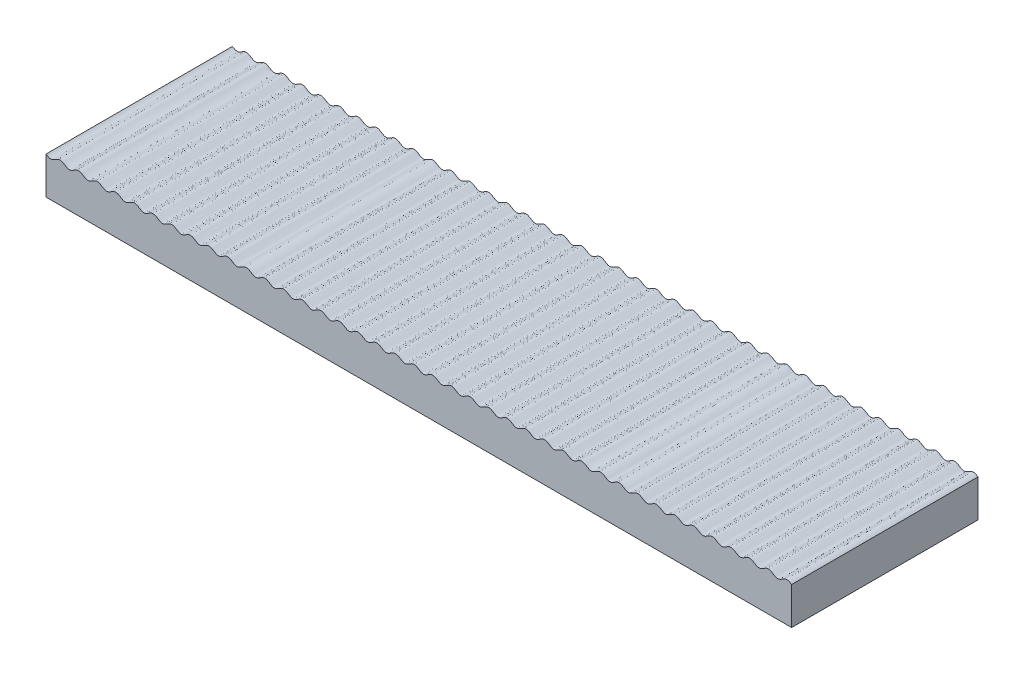
SolidWorks part; units mm, degrees
ref_plane "Ebene vorne" through (0, 0, 0) normal (0, 0, 1) x (1, 0, 0)
ref_plane "Ebene oben" through (0, 0, 0) normal (0, 1, 0) x (1, 0, 0)
ref_plane "Ebene rechts" through (0, 0, 0) normal (1, 0, 0) x (0, 0, -1)
sketch "Skizze1" plane through (0, 0, 0) normal (0, 0, 1) x (1, 0, 0)
  line L0 (0, 10) -> (0, 0)
  line L1 (0, 0) -> (200, 0)
  line L3 (0, 10) -> (200, 10) construction
  line L4 (200, 0) -> (200, 10)
  line L5 (0, 10) -> (0, 0) construction
  line L6 (5, 10) -> (5, 0) construction
  line L7 (0, 9.5001) -> (200, 9.5001) construction
  spline S0 degree 4 poles (-19.8, 9.8758) (-19.7067, 9.8176) (-19.5164, 9.7081) (-19.2314, 9.5662) (-18.8203, 9.473) (-18.326, 9.5323) (-17.8147, 9.7864) (-17.3529, 10.1027) (-16.8627, 10.3873) (-16.4131, 10.513) (-16.0482, 10.5034) (-15.6367, 10.3799) (-15.2035, 10.1377) (-14.7965, 9.8623) (-14.3634, 9.6201) (-13.955, 9.4976) (-13.5973, 9.4869) (-13.171, 9.601) (-12.7145, 9.855) (-12.2855, 10.145) (-11.829, 10.399) (-11.4027, 10.5131) (-11.045, 10.5024) (-10.6366, 10.3799) (-10.2035, 10.1377) (-9.7965, 9.8623) (-9.3634, 9.6201) (-8.955, 9.4976) (-8.5973, 9.4869) (-8.171, 9.601) (-7.7145, 9.855) (-7.2855, 10.145) (-6.829, 10.399) (-6.4027, 10.5131) (-6.045, 10.5024) (-5.6366, 10.3799) (-5.2035, 10.1377) (-4.7965, 9.8623) (-4.3634, 9.6201) (-3.955, 9.4975) (-3.5973, 9.487) (-3.2519, 9.5793) (-2.9327, 9.7338) (-2.6392, 9.9107) (-2.3608, 10.0893) (-2.0673, 10.2662) (-1.7482, 10.4208) (-1.4026, 10.513) (-1.0454, 10.5027) (-0.7134, 10.4022) (-0.4346, 10.2679) (-0.0875, 10.0567) (0.0877, 9.9432) (0.4351, 9.7318) (0.7141, 9.5976) (1.0465, 9.497) (1.404, 9.4872) (1.7498, 9.5798) (2.0691, 9.7348) (2.3628, 9.9119) (2.6415, 10.0907) (2.9353, 10.2676) (3.255, 10.422) (3.601, 10.5135) (3.959, 10.5018) (4.3673, 10.3781) (4.8005, 10.1351) (5.2078, 9.8594) (5.6418, 9.6176) (6.051, 9.4965) (6.4092, 9.4877) (6.8353, 9.6039) (7.2916, 9.859) (7.7209, 10.1492) (8.1785, 10.4025) (8.606, 10.5142) (8.964, 10.5009) (9.3719, 10.3759) (9.8047, 10.1324) (10.212, 9.8567) (10.6464, 9.6155) (11.0561, 9.4957) (11.4142, 9.4884) (11.8399, 9.606) (12.2958, 9.8617) (12.7251, 10.152) (13.1832, 10.4045) (13.6111, 10.5148) (13.969, 10.5) (14.3764, 10.3737) (14.8089, 10.1296) (15.2162, 9.854) (15.651, 9.6133) (16.0611, 9.4949) (16.4193, 9.4891) (16.8445, 9.6082) (17.3, 9.8645) (17.7293, 10.1547) (18.1878, 10.4066) (18.6162, 10.5154) (18.974, 10.4991) (19.381, 10.3715) (19.8131, 10.1269) (20.2204, 9.8512) (20.6556, 9.6112) (21.0661, 9.4941) (21.4243, 9.4899) (21.8491, 9.6103) (22.3042, 9.8672) (22.7335, 10.1574) (23.1924, 10.4087) (23.6213, 10.516) (23.979, 10.4981) (24.3855, 10.3693) (24.8172, 10.1241) (25.2246, 9.8485) (25.6602, 9.6091) (26.0711, 9.4933) (26.4294, 9.4906) (26.8537, 9.6125) (27.3084, 9.87) (27.7377, 10.1602) (28.1971, 10.4108) (28.6264, 10.5165) (28.984, 10.4971) (29.3901, 10.3671) (29.8214, 10.1214) (30.2288, 9.8458) (30.6648, 9.607) (31.0762, 9.4925) (31.4344, 9.4914) (31.8582, 9.6147) (32.3126, 9.8728) (32.7419, 10.1629) (33.2017, 10.4128) (33.6314, 10.5171) (33.989, 10.4961) (34.3946, 10.3649) (34.8256, 10.1186) (35.233, 9.843) (35.6694, 9.6049) (36.0812, 9.4918) (36.4394, 9.4922) (36.8628, 9.6168) (37.3167, 9.8755) (37.7461, 10.1656) (38.2064, 10.4149) (38.6365, 10.5176) (38.994, 10.4951) (39.3992, 10.3627) (39.8298, 10.1159) (40.2372, 9.8403) (40.674, 9.6028) (41.0862, 9.4911) (41.4445, 9.493) (41.8674, 9.619) (42.3209, 9.8783) (42.7503, 10.1684) (43.2111, 10.4169) (43.6416, 10.518) (43.9989, 10.4941) (44.4037, 10.3604) (44.834, 10.1131) (45.2413, 9.8375) (45.6786, 9.6008) (46.1029, 9.4872) (46.4863, 9.4959) (46.9217, 9.6444) (47.3795, 9.9177) (47.8057, 10.2028) (48.2505, 10.4305) (48.6813, 10.5212) (49.0593, 10.485) (49.4679, 10.3282) (49.8923, 10.073) (50.2896, 9.8093) (50.7003, 9.594) (51.0853, 9.4929) (51.4172, 9.4933) (51.802, 9.595) (52.2125, 9.8106) (52.6097, 10.0744) (53.0344, 10.3294) (53.4487, 10.4878) (53.8397, 10.5222) (54.2866, 10.4178) (54.7476, 10.1698) (55.177, 9.8796) (55.6304, 9.6201) (56.053, 9.4934) (56.4112, 9.4908) (56.8237, 9.6018) (57.2607, 9.839) (57.6681, 10.1145) (58.0986, 10.3616) (58.5036, 10.4946) (58.8609, 10.5178) (59.2913, 10.4159) (59.7518, 10.167) (60.1812, 9.8769) (60.6349, 9.6179) (61.058, 9.4926) (61.4163, 9.4915) (61.8283, 9.6038) (62.2649, 9.8417) (62.6723, 10.1172) (63.1031, 10.3638) (63.5085, 10.4956) (63.866, 10.5173) (64.2959, 10.4138) (64.756, 10.1643) (65.1854, 9.8741) (65.6395, 9.6157) (66.0631, 9.4918) (66.4213, 9.4922) (66.8329, 9.6059) (67.2691, 9.8444) (67.6765, 10.12) (68.1076, 10.366) (68.5135, 10.4966) (68.8711, 10.5168) (69.3006, 10.4118) (69.7602, 10.1615) (70.1895, 9.8714) (70.6441, 9.6136) (71.0681, 9.491) (71.4263, 9.4929) (71.8375, 9.608) (72.2733, 9.8471) (72.6807, 10.1227) (73.1122, 10.3682) (73.5185, 10.4976) (73.8762, 10.5163) (74.3052, 10.4097) (74.7644, 10.1588) (75.1937, 9.8686) (75.6486, 9.6114) (76.0732, 9.4903) (76.4314, 9.4937) (76.8421, 9.6101) (77.2775, 9.8499) (77.6848, 10.1255) (78.1167, 10.3704) (78.5235, 10.4986) (78.8813, 10.5157) (79.3099, 10.4077) (79.7686, 10.1561) (80.1979, 9.8659) (80.6532, 9.6092) (81.0782, 9.4895) (81.4364, 9.4945) (81.8467, 9.6123) (82.2817, 9.8526) (82.689, 10.1282) (83.1213, 10.3726) (83.5285, 10.4995) (83.8863, 10.5151) (84.3145, 10.4056) (84.7728, 10.1533) (85.2021, 9.8631) (85.6578, 9.6071) (86.0833, 9.4888) (86.4414, 9.4953) (86.8513, 9.6144) (87.2859, 9.8553) (87.6932, 10.131) (88.1258, 10.3748) (88.5335, 10.5004) (88.8914, 10.5145) (89.3192, 10.4035) (89.777, 10.1506) (90.2063, 9.8604) (90.6624, 9.605) (91.0883, 9.4881) (91.4464, 9.4961) (91.8559, 9.6165) (92.2901, 9.8581) (92.6974, 10.1337) (93.1304, 10.377) (93.5385, 10.5013) (93.8965, 10.5139) (94.3238, 10.4014) (94.7812, 10.1479) (95.2105, 9.8576) (95.667, 9.6028) (96.0934, 9.4874) (96.4515, 9.4969) (96.8605, 9.6187) (97.2943, 9.8608) (97.7016, 10.1365) (98.135, 10.3792) (98.5435, 10.5022) (98.9016, 10.5133) (99.3284, 10.3993) (99.7854, 10.1451) (100.2146, 9.8549) (100.6716, 9.6007) (101.0984, 9.4867) (101.4565, 9.4978) (101.865, 9.6208) (102.2984, 9.8635) (102.7057, 10.1392) (103.1395, 10.3813) (103.5485, 10.5031) (103.9066, 10.5126) (104.333, 10.3972) (104.7895, 10.1424) (105.2188, 9.8521) (105.6762, 9.5986) (106.1035, 9.4861) (106.4615, 9.4987) (106.8696, 9.623) (107.3026, 9.8663) (107.7099, 10.1419) (108.1441, 10.3835) (108.5536, 10.5039) (108.9117, 10.5119) (109.3376, 10.395) (109.7937, 10.1396) (110.223, 9.8494) (110.6808, 9.5965) (111.1086, 9.4855) (111.4665, 9.4996) (111.8742, 9.6252) (112.3068, 9.869) (112.7141, 10.1447) (113.1487, 10.3856) (113.5586, 10.5047) (113.9167, 10.5112) (114.3422, 10.3929) (114.7979, 10.1369) (115.2272, 9.8467) (115.6855, 9.5944) (116.1137, 9.4849) (116.4715, 9.5005) (116.8787, 9.6274) (117.311, 9.8718) (117.7183, 10.1474) (118.1533, 10.3877) (118.5636, 10.5055) (118.9218, 10.5105) (119.3468, 10.3908) (119.8021, 10.1341) (120.2314, 9.8439) (120.6901, 9.5923) (121.1187, 9.4843) (121.4765, 9.5014) (121.8833, 9.6296) (122.3152, 9.8745) (122.7225, 10.1501) (123.1579, 10.3899) (123.5686, 10.5063) (123.9268, 10.5097) (124.3514, 10.3886) (124.8063, 10.1314) (125.2356, 9.8412) (125.6948, 9.5903) (126.1238, 9.4837) (126.4815, 9.5024) (126.8878, 9.6318) (127.3193, 9.8773) (127.7267, 10.1529) (128.1625, 10.392) (128.5737, 10.5071) (128.9319, 10.509) (129.3559, 10.3864) (129.8105, 10.1286) (130.2398, 9.8385) (130.6994, 9.5882) (131.1289, 9.4832) (131.4865, 9.5034) (131.8924, 9.634) (132.3235, 9.88) (132.7309, 10.1556) (133.1671, 10.3941) (133.5787, 10.5078) (133.9369, 10.5082) (134.3605, 10.3843) (134.8146, 10.1259) (135.244, 9.8357) (135.7041, 9.5862) (136.134, 9.4827) (136.4915, 9.5044) (136.8969, 9.6362) (137.3277, 9.8828) (137.7351, 10.1583) (138.1717, 10.3962) (138.5837, 10.5085) (138.942, 10.5074) (139.3651, 10.3821) (139.8188, 10.1231) (140.2482, 9.833) (140.7087, 9.5841) (141.1391, 9.4822) (141.4964, 9.5054) (141.9014, 9.6384) (142.3319, 9.8855) (142.7393, 10.161) (143.1763, 10.3982) (143.5888, 10.5092) (143.947, 10.5066) (144.3696, 10.3799) (144.823, 10.1204) (145.2524, 9.8302) (145.7134, 9.5822) (146.1603, 9.4778) (146.5513, 9.5122) (146.8958, 9.6439) (147.1989, 9.8107) (147.4712, 9.9815) (147.7219, 10.1405) (147.9858, 10.2935) (148.2704, 10.4242) (148.5828, 10.5067) (148.9147, 10.5071) (149.2997, 10.406) (149.7104, 10.1907) (150.1076, 9.927) (150.5321, 9.6718) (150.9407, 9.515) (151.3187, 9.4788) (151.7495, 9.5695) (152.1943, 9.7972) (152.6205, 10.0823) (153.0783, 10.3556) (153.5137, 10.5041) (153.8971, 10.5128) (154.3214, 10.3992) (154.7587, 10.1625) (155.166, 9.8869) (155.5963, 9.6396) (156.0011, 9.5059) (156.3584, 9.482) (156.7889, 9.5831) (157.2497, 9.8316) (157.6791, 10.1217) (158.1326, 10.381) (158.5555, 10.507) (158.9138, 10.5089) (159.326, 10.3972) (159.7628, 10.1597) (160.1702, 9.8841) (160.6008, 9.6373) (161.006, 9.5049) (161.3635, 9.4824) (161.7936, 9.5851) (162.2539, 9.8344) (162.6833, 10.1245) (163.1372, 10.3832) (163.5606, 10.5078) (163.9188, 10.5082) (164.3306, 10.3951) (164.767, 10.157) (165.1744, 9.8814) (165.6054, 9.6351) (166.011, 9.5039) (166.3686, 9.4829) (166.7983, 9.5872) (167.2581, 9.8371) (167.6874, 10.1272) (168.1418, 10.3853) (168.5656, 10.5086) (168.9238, 10.5075) (169.3352, 10.393) (169.7712, 10.1542) (170.1786, 9.8786) (170.6099, 9.6329) (171.016, 9.5029) (171.3736, 9.4835) (171.8029, 9.5892) (172.2623, 9.8398) (172.6916, 10.13) (173.1463, 10.3875) (173.5706, 10.5094) (173.9289, 10.5067) (174.3398, 10.3909) (174.7754, 10.1515) (175.1828, 9.8759) (175.6145, 9.6307) (176.021, 9.5019) (176.3787, 9.484) (176.8076, 9.5913) (177.2665, 9.8426) (177.6958, 10.1328) (178.1509, 10.3897) (178.5757, 10.5101) (178.9339, 10.5059) (179.3444, 10.3888) (179.7796, 10.1488) (180.1869, 9.8731) (180.619, 9.6285) (181.026, 9.5009) (181.3838, 9.4846) (181.8122, 9.5934) (182.2707, 9.8453) (182.7, 10.1355) (183.1555, 10.3918) (183.5807, 10.5109) (183.9389, 10.5051) (184.349, 10.3867) (184.7838, 10.146) (185.1911, 9.8704) (185.6236, 9.6263) (186.031, 9.5) (186.3889, 9.4852) (186.8168, 9.5955) (187.2749, 9.848) (187.7042, 10.1383) (188.1601, 10.394) (188.5858, 10.5116) (188.9439, 10.5043) (189.3536, 10.3845) (189.788, 10.1433) (190.1953, 9.8676) (190.6281, 9.6241) (191.036, 9.4991) (191.394, 9.4858) (191.8215, 9.5975) (192.2791, 9.8508) (192.7084, 10.141) (193.1647, 10.3961) (193.5908, 10.5123) (193.949, 10.5035) (194.3582, 10.3824) (194.7922, 10.1406) (195.1995, 9.8649) (195.6327, 9.6219) (196.041, 9.4982) (196.399, 9.4865) (196.745, 9.578) (197.0647, 9.7324) (197.3585, 9.9093) (197.6372, 10.0881) (197.9309, 10.2652) (198.2502, 10.4202) (198.596, 10.5128) (198.9535, 10.503) (199.2859, 10.4024) (199.5649, 10.2682) (199.9123, 10.0568) (200.0875, 9.9433) (200.4346, 9.7321) (200.7134, 9.5978) (201.0454, 9.4973) (201.4026, 9.487) (201.7482, 9.5792) (202.0673, 9.7338) (202.3608, 9.9107) (202.6392, 10.0893) (202.9327, 10.2662) (203.2519, 10.4207) (203.5973, 10.513) (203.955, 10.5025) (204.3634, 10.3799) (204.7965, 10.1377) (205.2035, 9.8623) (205.6366, 9.6201) (206.045, 9.4976) (206.4027, 9.4869) (206.829, 9.601) (207.2855, 9.855) (207.7145, 10.145) (208.171, 10.399) (208.5973, 10.5131) (208.955, 10.5024) (209.3634, 10.3799) (209.7965, 10.1377) (210.2035, 9.8623) (210.6366, 9.6201) (211.045, 9.4976) (211.4027, 9.4869) (211.829, 9.601) (212.2855, 9.855) (212.7145, 10.145) (213.171, 10.399) (213.5973, 10.5131) (213.955, 10.5024) (214.3634, 10.3799) (214.7965, 10.1377) (215.2035, 9.8623) (215.6367, 9.6201) (216.0482, 9.4966) (216.4131, 9.487) (216.8627, 9.6127) (217.3529, 9.8973) (217.8147, 10.2136) (218.326, 10.4677) (218.8203, 10.527) (219.2314, 10.4338) (219.5164, 10.2919) (219.7067, 10.1824) (219.8, 10.1242) knots 0 0 0 0 0 0.001678 0.003357 0.004848 0.006339 0.00915 0.011962 0.013453 0.014944 0.016201 0.017457 0.019971 0.022484 0.023741 0.024997 0.026437 0.027876 0.030406 0.032936 0.034376 0.035815 0.037072 0.038328 0.040842 0.043355 0.044611 0.045868 0.047308 0.048747 0.051277 0.053807 0.055246 0.056686 0.057942 0.059199 0.061712 0.064226 0.065482 0.066739 0.068178 0.069618 0.070883 0.072148 0.073413 0.074678 0.076117 0.077557 0.078813 0.08007 0.081327 0.082583 0.083841 0.085099 0.086357 0.087614 0.089055 0.090496 0.091762 0.093028 0.094294 0.095561 0.097001 0.098442 0.0997 0.100958 0.103473 0.105989 0.107247 0.108504 0.109945 0.111386 0.113918 0.116451 0.117891 0.119332 0.12059 0.121848 0.124363 0.126879 0.128137 0.129394 0.130835 0.132276 0.134808 0.137341 0.138781 0.140222 0.14148 0.142738 0.145253 0.147769 0.149027 0.150284 0.151725 0.153166 0.155698 0.158231 0.159671 0.161112 0.16237 0.163628 0.166143 0.168659 0.169916 0.171174 0.172615 0.174056 0.176588 0.179121 0.180561 0.182002 0.18326 0.184517 0.187033 0.189549 0.190806 0.192064 0.193505 0.194946 0.197478 0.200011 0.201451 0.202892 0.20415 0.205407 0.207923 0.210439 0.211696 0.212954 0.214395 0.215836 0.218368 0.220901 0.222341 0.223782 0.22504 0.226297 0.228813 0.231329 0.232586 0.233844 0.235285 0.236726 0.239258 0.241791 0.243231 0.244672 0.24593 0.247187 0.249703 0.252218 0.253476 0.254734 0.256175 0.257616 0.260148 0.262681 0.264121 0.265562 0.26682 0.268077 0.270593 0.273108 0.274366 0.275624 0.277248 0.278872 0.281313 0.283753 0.285102 0.286451 0.287959 0.289467 0.291737 0.294007 0.295261 0.296514 0.297767 0.29902 0.30129 0.303561 0.305068 0.306576 0.308017 0.309458 0.31199 0.314522 0.315963 0.317404 0.318662 0.31992 0.322435 0.324951 0.326209 0.327466 0.328907 0.330348 0.33288 0.335412 0.336853 0.338294 0.339552 0.34081 0.343325 0.345841 0.347099 0.348356 0.349797 0.351238 0.35377 0.356302 0.357743 0.359184 0.360442 0.3617 0.364215 0.366731 0.367989 0.369246 0.370687 0.372128 0.37466 0.377192 0.378633 0.380074 0.381332 0.38259 0.385105 0.387621 0.388879 0.390136 0.391577 0.393018 0.39555 0.398082 0.399523 0.400964 0.402222 0.40348 0.405995 0.408511 0.409769 0.411026 0.412467 0.413908 0.41644 0.418972 0.420413 0.421854 0.423112 0.42437 0.426885 0.429401 0.430658 0.431916 0.433357 0.434798 0.43733 0.439862 0.441303 0.442744 0.444002 0.44526 0.447775 0.450291 0.451548 0.452806 0.454247 0.455688 0.45822 0.460752 0.462193 0.463634 0.464892 0.466149 0.468665 0.471181 0.472438 0.473696 0.475137 0.476578 0.47911 0.481642 0.483083 0.484524 0.485782 0.487039 0.489555 0.492071 0.493328 0.494586 0.496027 0.497468 0.5 0.502532 0.503973 0.505414 0.506672 0.507929 0.510445 0.512961 0.514218 0.515476 0.516917 0.518358 0.52089 0.523422 0.524863 0.526304 0.527562 0.528819 0.531335 0.533851 0.535108 0.536366 0.537807 0.539248 0.54178 0.544312 0.545753 0.547194 0.548452 0.549709 0.552225 0.55474 0.555998 0.557256 0.558697 0.560138 0.56267 0.565202 0.566643 0.568084 0.569342 0.570599 0.573115 0.57563 0.576888 0.578146 0.579587 0.581028 0.58356 0.586092 0.587533 0.588974 0.590231 0.591489 0.594005 0.59652 0.597778 0.599036 0.600477 0.601918 0.60445 0.606982 0.608423 0.609864 0.611121 0.612379 0.614895 0.61741 0.618668 0.619926 0.621367 0.622808 0.62534 0.627872 0.629313 0.630754 0.632011 0.633269 0.635785 0.6383 0.639558 0.640816 0.642257 0.643698 0.64623 0.648762 0.650203 0.651644 0.652901 0.654159 0.656675 0.65919 0.660448 0.661706 0.663147 0.664588 0.66712 0.669652 0.671093 0.672534 0.673791 0.675049 0.677565 0.68008 0.681338 0.682596 0.684037 0.685478 0.68801 0.690542 0.691983 0.693424 0.694932 0.696439 0.697575 0.69871 0.699845 0.70098 0.702233 0.703486 0.704739 0.705993 0.708263 0.710533 0.712041 0.713549 0.714898 0.716247 0.718687 0.721128 0.722752 0.724376 0.725634 0.726892 0.729407 0.731923 0.73318 0.734438 0.735879 0.737319 0.739852 0.742384 0.743825 0.745266 0.746524 0.747782 0.750297 0.752813 0.75407 0.755328 0.756769 0.758209 0.760742 0.763274 0.764715 0.766156 0.767414 0.768671 0.771187 0.773703 0.77496 0.776218 0.777659 0.779099 0.781632 0.784164 0.785605 0.787046 0.788304 0.789561 0.792077 0.794593 0.79585 0.797108 0.798549 0.799989 0.802522 0.805054 0.806495 0.807936 0.809194 0.810451 0.812967 0.815483 0.81674 0.817998 0.819439 0.820879 0.823412 0.825944 0.827385 0.828826 0.830084 0.831341 0.833857 0.836372 0.83763 0.838888 0.840329 0.841769 0.844302 0.846834 0.848275 0.849716 0.850973 0.852231 0.854747 0.857262 0.85852 0.859778 0.861219 0.862659 0.865192 0.867724 0.869165 0.870606 0.871863 0.873121 0.875637 0.878152 0.87941 0.880668 0.882109 0.883549 0.886082 0.888614 0.890055 0.891496 0.892753 0.894011 0.896527 0.899042 0.9003 0.901558 0.902999 0.904439 0.905706 0.906972 0.908238 0.909504 0.910945 0.912386 0.913643 0.914901 0.916159 0.917417 0.918673 0.91993 0.921187 0.922443 0.923883 0.925322 0.926587 0.927852 0.929117 0.930382 0.931822 0.933261 0.934518 0.935774 0.938288 0.940801 0.942058 0.943314 0.944754 0.946193 0.948723 0.951253 0.952692 0.954132 0.955389 0.956645 0.959158 0.961672 0.962928 0.964185 0.965624 0.967064 0.969594 0.972124 0.973563 0.975003 0.976259 0.977516 0.980029 0.982543 0.983799 0.985056 0.986547 0.988038 0.99085 0.993661 0.995152 0.996643 0.998322 1 1 1 1 1 construction
  spline S1 degree 4 poles (0, 10) (0.0582, 9.9635) (0.1745, 9.8904) (0.4351, 9.7318) (0.7141, 9.5976) (1.0465, 9.497) (1.404, 9.4872) (1.7498, 9.5798) (2.0691, 9.7348) (2.3628, 9.9119) (2.6415, 10.0907) (2.9353, 10.2676) (3.255, 10.422) (3.601, 10.5135) (3.959, 10.5018) (4.3673, 10.3781) (4.8005, 10.1351) (5.2078, 9.8594) (5.6418, 9.6176) (6.051, 9.4965) (6.4092, 9.4877) (6.8353, 9.6039) (7.2916, 9.859) (7.7209, 10.1492) (8.1785, 10.4025) (8.606, 10.5142) (8.964, 10.5009) (9.3719, 10.3759) (9.8047, 10.1324) (10.212, 9.8567) (10.6464, 9.6155) (11.0561, 9.4957) (11.4142, 9.4884) (11.8399, 9.606) (12.2958, 9.8617) (12.7251, 10.152) (13.1832, 10.4045) (13.6111, 10.5148) (13.969, 10.5) (14.3764, 10.3737) (14.8089, 10.1296) (15.2162, 9.854) (15.651, 9.6133) (16.0611, 9.4949) (16.4193, 9.4891) (16.8445, 9.6082) (17.3, 9.8645) (17.7293, 10.1547) (18.1878, 10.4066) (18.6162, 10.5154) (18.974, 10.4991) (19.381, 10.3715) (19.8131, 10.1269) (20.2204, 9.8512) (20.6556, 9.6112) (21.0661, 9.4941) (21.4243, 9.4899) (21.8491, 9.6103) (22.3042, 9.8672) (22.7335, 10.1574) (23.1924, 10.4087) (23.6213, 10.516) (23.979, 10.4981) (24.3855, 10.3693) (24.8172, 10.1241) (25.2246, 9.8485) (25.6602, 9.6091) (26.0711, 9.4933) (26.4294, 9.4906) (26.8537, 9.6125) (27.3084, 9.87) (27.7377, 10.1602) (28.1971, 10.4108) (28.6264, 10.5165) (28.984, 10.4971) (29.3901, 10.3671) (29.8214, 10.1214) (30.2288, 9.8458) (30.6648, 9.607) (31.0762, 9.4925) (31.4344, 9.4914) (31.8582, 9.6147) (32.3126, 9.8728) (32.7419, 10.1629) (33.2017, 10.4128) (33.6314, 10.5171) (33.989, 10.4961) (34.3946, 10.3649) (34.8256, 10.1186) (35.233, 9.843) (35.6694, 9.6049) (36.0812, 9.4918) (36.4394, 9.4922) (36.8628, 9.6168) (37.3167, 9.8755) (37.7461, 10.1656) (38.2064, 10.4149) (38.6365, 10.5176) (38.994, 10.4951) (39.3992, 10.3627) (39.8298, 10.1159) (40.2372, 9.8403) (40.674, 9.6028) (41.0862, 9.4911) (41.4445, 9.493) (41.8674, 9.619) (42.3209, 9.8783) (42.7503, 10.1684) (43.2111, 10.4169) (43.6416, 10.518) (43.9989, 10.4941) (44.4037, 10.3604) (44.834, 10.1131) (45.2413, 9.8375) (45.6786, 9.6008) (46.1029, 9.4872) (46.4863, 9.4959) (46.9217, 9.6444) (47.3795, 9.9177) (47.8057, 10.2028) (48.2505, 10.4305) (48.6813, 10.5212) (49.0593, 10.485) (49.4679, 10.3282) (49.8923, 10.073) (50.2896, 9.8093) (50.7003, 9.594) (51.0853, 9.4929) (51.4172, 9.4933) (51.802, 9.595) (52.2125, 9.8106) (52.6097, 10.0744) (53.0344, 10.3294) (53.4487, 10.4878) (53.8397, 10.5222) (54.2866, 10.4178) (54.7476, 10.1698) (55.177, 9.8796) (55.6304, 9.6201) (56.053, 9.4934) (56.4112, 9.4908) (56.8237, 9.6018) (57.2607, 9.839) (57.6681, 10.1145) (58.0986, 10.3616) (58.5036, 10.4946) (58.8609, 10.5178) (59.2913, 10.4159) (59.7518, 10.167) (60.1812, 9.8769) (60.6349, 9.6179) (61.058, 9.4926) (61.4163, 9.4915) (61.8283, 9.6038) (62.2649, 9.8417) (62.6723, 10.1172) (63.1031, 10.3638) (63.5085, 10.4956) (63.866, 10.5173) (64.2959, 10.4138) (64.756, 10.1643) (65.1854, 9.8741) (65.6395, 9.6157) (66.0631, 9.4918) (66.4213, 9.4922) (66.8329, 9.6059) (67.2691, 9.8444) (67.6765, 10.12) (68.1076, 10.366) (68.5135, 10.4966) (68.8711, 10.5168) (69.3006, 10.4118) (69.7602, 10.1615) (70.1895, 9.8714) (70.6441, 9.6136) (71.0681, 9.491) (71.4263, 9.4929) (71.8375, 9.608) (72.2733, 9.8471) (72.6807, 10.1227) (73.1122, 10.3682) (73.5185, 10.4976) (73.8762, 10.5163) (74.3052, 10.4097) (74.7644, 10.1588) (75.1937, 9.8686) (75.6486, 9.6114) (76.0732, 9.4903) (76.4314, 9.4937) (76.8421, 9.6101) (77.2775, 9.8499) (77.6848, 10.1255) (78.1167, 10.3704) (78.5235, 10.4986) (78.8813, 10.5157) (79.3099, 10.4077) (79.7686, 10.1561) (80.1979, 9.8659) (80.6532, 9.6092) (81.0782, 9.4895) (81.4364, 9.4945) (81.8467, 9.6123) (82.2817, 9.8526) (82.689, 10.1282) (83.1213, 10.3726) (83.5285, 10.4995) (83.8863, 10.5151) (84.3145, 10.4056) (84.7728, 10.1533) (85.2021, 9.8631) (85.6578, 9.6071) (86.0833, 9.4888) (86.4414, 9.4953) (86.8513, 9.6144) (87.2859, 9.8553) (87.6932, 10.131) (88.1258, 10.3748) (88.5335, 10.5004) (88.8914, 10.5145) (89.3192, 10.4035) (89.777, 10.1506) (90.2063, 9.8604) (90.6624, 9.605) (91.0883, 9.4881) (91.4464, 9.4961) (91.8559, 9.6165) (92.2901, 9.8581) (92.6974, 10.1337) (93.1304, 10.377) (93.5385, 10.5013) (93.8965, 10.5139) (94.3238, 10.4014) (94.7812, 10.1479) (95.2105, 9.8576) (95.667, 9.6028) (96.0934, 9.4874) (96.4515, 9.4969) (96.8605, 9.6187) (97.2943, 9.8608) (97.7016, 10.1365) (98.135, 10.3792) (98.5435, 10.5022) (98.9016, 10.5133) (99.3284, 10.3993) (99.7854, 10.1451) (100.2146, 9.8549) (100.6716, 9.6007) (101.0984, 9.4867) (101.4565, 9.4978) (101.865, 9.6208) (102.2984, 9.8635) (102.7057, 10.1392) (103.1395, 10.3813) (103.5485, 10.5031) (103.9066, 10.5126) (104.333, 10.3972) (104.7895, 10.1424) (105.2188, 9.8521) (105.6762, 9.5986) (106.1035, 9.4861) (106.4615, 9.4987) (106.8696, 9.623) (107.3026, 9.8663) (107.7099, 10.1419) (108.1441, 10.3835) (108.5536, 10.5039) (108.9117, 10.5119) (109.3376, 10.395) (109.7937, 10.1396) (110.223, 9.8494) (110.6808, 9.5965) (111.1086, 9.4855) (111.4665, 9.4996) (111.8742, 9.6252) (112.3068, 9.869) (112.7141, 10.1447) (113.1487, 10.3856) (113.5586, 10.5047) (113.9167, 10.5112) (114.3422, 10.3929) (114.7979, 10.1369) (115.2272, 9.8467) (115.6855, 9.5944) (116.1137, 9.4849) (116.4715, 9.5005) (116.8787, 9.6274) (117.311, 9.8718) (117.7183, 10.1474) (118.1533, 10.3877) (118.5636, 10.5055) (118.9218, 10.5105) (119.3468, 10.3908) (119.8021, 10.1341) (120.2314, 9.8439) (120.6901, 9.5923) (121.1187, 9.4843) (121.4765, 9.5014) (121.8833, 9.6296) (122.3152, 9.8745) (122.7225, 10.1501) (123.1579, 10.3899) (123.5686, 10.5063) (123.9268, 10.5097) (124.3514, 10.3886) (124.8063, 10.1314) (125.2356, 9.8412) (125.6948, 9.5903) (126.1238, 9.4837) (126.4815, 9.5024) (126.8878, 9.6318) (127.3193, 9.8773) (127.7267, 10.1529) (128.1625, 10.392) (128.5737, 10.5071) (128.9319, 10.509) (129.3559, 10.3864) (129.8105, 10.1286) (130.2398, 9.8385) (130.6994, 9.5882) (131.1289, 9.4832) (131.4865, 9.5034) (131.8924, 9.634) (132.3235, 9.88) (132.7309, 10.1556) (133.1671, 10.3941) (133.5787, 10.5078) (133.9369, 10.5082) (134.3605, 10.3843) (134.8146, 10.1259) (135.244, 9.8357) (135.7041, 9.5862) (136.134, 9.4827) (136.4915, 9.5044) (136.8969, 9.6362) (137.3277, 9.8828) (137.7351, 10.1583) (138.1717, 10.3962) (138.5837, 10.5085) (138.942, 10.5074) (139.3651, 10.3821) (139.8188, 10.1231) (140.2482, 9.833) (140.7087, 9.5841) (141.1391, 9.4822) (141.4964, 9.5054) (141.9014, 9.6384) (142.3319, 9.8855) (142.7393, 10.161) (143.1763, 10.3982) (143.5888, 10.5092) (143.947, 10.5066) (144.3696, 10.3799) (144.823, 10.1204) (145.2524, 9.8302) (145.7134, 9.5822) (146.1603, 9.4778) (146.5513, 9.5122) (146.8958, 9.6439) (147.1989, 9.8107) (147.4712, 9.9815) (147.7219, 10.1405) (147.9858, 10.2935) (148.2704, 10.4242) (148.5828, 10.5067) (148.9147, 10.5071) (149.2997, 10.406) (149.7104, 10.1907) (150.1076, 9.927) (150.5321, 9.6718) (150.9407, 9.515) (151.3187, 9.4788) (151.7495, 9.5695) (152.1943, 9.7972) (152.6205, 10.0823) (153.0783, 10.3556) (153.5137, 10.5041) (153.8971, 10.5128) (154.3214, 10.3992) (154.7587, 10.1625) (155.166, 9.8869) (155.5963, 9.6396) (156.0011, 9.5059) (156.3584, 9.482) (156.7889, 9.5831) (157.2497, 9.8316) (157.6791, 10.1217) (158.1326, 10.381) (158.5555, 10.507) (158.9138, 10.5089) (159.326, 10.3972) (159.7628, 10.1597) (160.1702, 9.8841) (160.6008, 9.6373) (161.006, 9.5049) (161.3635, 9.4824) (161.7936, 9.5851) (162.2539, 9.8344) (162.6833, 10.1245) (163.1372, 10.3832) (163.5606, 10.5078) (163.9188, 10.5082) (164.3306, 10.3951) (164.767, 10.157) (165.1744, 9.8814) (165.6054, 9.6351) (166.011, 9.5039) (166.3686, 9.4829) (166.7983, 9.5872) (167.2581, 9.8371) (167.6874, 10.1272) (168.1418, 10.3853) (168.5656, 10.5086) (168.9238, 10.5075) (169.3352, 10.393) (169.7712, 10.1542) (170.1786, 9.8786) (170.6099, 9.6329) (171.016, 9.5029) (171.3736, 9.4835) (171.8029, 9.5892) (172.2623, 9.8398) (172.6916, 10.13) (173.1463, 10.3875) (173.5706, 10.5094) (173.9289, 10.5067) (174.3398, 10.3909) (174.7754, 10.1515) (175.1828, 9.8759) (175.6145, 9.6307) (176.021, 9.5019) (176.3787, 9.484) (176.8076, 9.5913) (177.2665, 9.8426) (177.6958, 10.1328) (178.1509, 10.3897) (178.5757, 10.5101) (178.9339, 10.5059) (179.3444, 10.3888) (179.7796, 10.1488) (180.1869, 9.8731) (180.619, 9.6285) (181.026, 9.5009) (181.3838, 9.4846) (181.8122, 9.5934) (182.2707, 9.8453) (182.7, 10.1355) (183.1555, 10.3918) (183.5807, 10.5109) (183.9389, 10.5051) (184.349, 10.3867) (184.7838, 10.146) (185.1911, 9.8704) (185.6236, 9.6263) (186.031, 9.5) (186.3889, 9.4852) (186.8168, 9.5955) (187.2749, 9.848) (187.7042, 10.1383) (188.1601, 10.394) (188.5858, 10.5116) (188.9439, 10.5043) (189.3536, 10.3845) (189.788, 10.1433) (190.1953, 9.8676) (190.6281, 9.6241) (191.036, 9.4991) (191.394, 9.4858) (191.8215, 9.5975) (192.2791, 9.8508) (192.7084, 10.141) (193.1647, 10.3961) (193.5908, 10.5123) (193.949, 10.5035) (194.3582, 10.3824) (194.7922, 10.1406) (195.1995, 9.8649) (195.6327, 9.6219) (196.041, 9.4982) (196.399, 9.4865) (196.745, 9.578) (197.0647, 9.7324) (197.3585, 9.9093) (197.6372, 10.0881) (197.9309, 10.2652) (198.2502, 10.4202) (198.596, 10.5128) (198.9535, 10.503) (199.2859, 10.4024) (199.5649, 10.2682) (199.8255, 10.1096) (199.9418, 10.0365) (200, 10) knots 0.082583 0.082583 0.082583 0.082583 0.082583 0.083841 0.085099 0.086357 0.087614 0.089055 0.090496 0.091762 0.093028 0.094294 0.095561 0.097001 0.098442 0.0997 0.100958 0.103473 0.105989 0.107247 0.108504 0.109945 0.111386 0.113918 0.116451 0.117891 0.119332 0.12059 0.121848 0.124363 0.126879 0.128137 0.129394 0.130835 0.132276 0.134808 0.137341 0.138781 0.140222 0.14148 0.142738 0.145253 0.147769 0.149027 0.150284 0.151725 0.153166 0.155698 0.158231 0.159671 0.161112 0.16237 0.163628 0.166143 0.168659 0.169916 0.171174 0.172615 0.174056 0.176588 0.179121 0.180561 0.182002 0.18326 0.184517 0.187033 0.189549 0.190806 0.192064 0.193505 0.194946 0.197478 0.200011 0.201451 0.202892 0.20415 0.205407 0.207923 0.210439 0.211696 0.212954 0.214395 0.215836 0.218368 0.220901 0.222341 0.223782 0.22504 0.226297 0.228813 0.231329 0.232586 0.233844 0.235285 0.236726 0.239258 0.241791 0.243231 0.244672 0.24593 0.247187 0.249703 0.252218 0.253476 0.254734 0.256175 0.257616 0.260148 0.262681 0.264121 0.265562 0.26682 0.268077 0.270593 0.273108 0.274366 0.275624 0.277248 0.278872 0.281313 0.283753 0.285102 0.286451 0.287959 0.289467 0.291737 0.294007 0.295261 0.296514 0.297767 0.29902 0.30129 0.303561 0.305068 0.306576 0.308017 0.309458 0.31199 0.314522 0.315963 0.317404 0.318662 0.31992 0.322435 0.324951 0.326209 0.327466 0.328907 0.330348 0.33288 0.335412 0.336853 0.338294 0.339552 0.34081 0.343325 0.345841 0.347099 0.348356 0.349797 0.351238 0.35377 0.356302 0.357743 0.359184 0.360442 0.3617 0.364215 0.366731 0.367989 0.369246 0.370687 0.372128 0.37466 0.377192 0.378633 0.380074 0.381332 0.38259 0.385105 0.387621 0.388879 0.390136 0.391577 0.393018 0.39555 0.398082 0.399523 0.400964 0.402222 0.40348 0.405995 0.408511 0.409769 0.411026 0.412467 0.413908 0.41644 0.418972 0.420413 0.421854 0.423112 0.42437 0.426885 0.429401 0.430658 0.431916 0.433357 0.434798 0.43733 0.439862 0.441303 0.442744 0.444002 0.44526 0.447775 0.450291 0.451548 0.452806 0.454247 0.455688 0.45822 0.460752 0.462193 0.463634 0.464892 0.466149 0.468665 0.471181 0.472438 0.473696 0.475137 0.476578 0.47911 0.481642 0.483083 0.484524 0.485782 0.487039 0.489555 0.492071 0.493328 0.494586 0.496027 0.497468 0.5 0.502532 0.503973 0.505414 0.506672 0.507929 0.510445 0.512961 0.514218 0.515476 0.516917 0.518358 0.52089 0.523422 0.524863 0.526304 0.527562 0.528819 0.531335 0.533851 0.535108 0.536366 0.537807 0.539248 0.54178 0.544312 0.545753 0.547194 0.548452 0.549709 0.552225 0.55474 0.555998 0.557256 0.558697 0.560138 0.56267 0.565202 0.566643 0.568084 0.569342 0.570599 0.573115 0.57563 0.576888 0.578146 0.579587 0.581028 0.58356 0.586092 0.587533 0.588974 0.590231 0.591489 0.594005 0.59652 0.597778 0.599036 0.600477 0.601918 0.60445 0.606982 0.608423 0.609864 0.611121 0.612379 0.614895 0.61741 0.618668 0.619926 0.621367 0.622808 0.62534 0.627872 0.629313 0.630754 0.632011 0.633269 0.635785 0.6383 0.639558 0.640816 0.642257 0.643698 0.64623 0.648762 0.650203 0.651644 0.652901 0.654159 0.656675 0.65919 0.660448 0.661706 0.663147 0.664588 0.66712 0.669652 0.671093 0.672534 0.673791 0.675049 0.677565 0.68008 0.681338 0.682596 0.684037 0.685478 0.68801 0.690542 0.691983 0.693424 0.694932 0.696439 0.697575 0.69871 0.699845 0.70098 0.702233 0.703486 0.704739 0.705993 0.708263 0.710533 0.712041 0.713549 0.714898 0.716247 0.718687 0.721128 0.722752 0.724376 0.725634 0.726892 0.729407 0.731923 0.73318 0.734438 0.735879 0.737319 0.739852 0.742384 0.743825 0.745266 0.746524 0.747782 0.750297 0.752813 0.75407 0.755328 0.756769 0.758209 0.760742 0.763274 0.764715 0.766156 0.767414 0.768671 0.771187 0.773703 0.77496 0.776218 0.777659 0.779099 0.781632 0.784164 0.785605 0.787046 0.788304 0.789561 0.792077 0.794593 0.79585 0.797108 0.798549 0.799989 0.802522 0.805054 0.806495 0.807936 0.809194 0.810451 0.812967 0.815483 0.81674 0.817998 0.819439 0.820879 0.823412 0.825944 0.827385 0.828826 0.830084 0.831341 0.833857 0.836372 0.83763 0.838888 0.840329 0.841769 0.844302 0.846834 0.848275 0.849716 0.850973 0.852231 0.854747 0.857262 0.85852 0.859778 0.861219 0.862659 0.865192 0.867724 0.869165 0.870606 0.871863 0.873121 0.875637 0.878152 0.87941 0.880668 0.882109 0.883549 0.886082 0.888614 0.890055 0.891496 0.892753 0.894011 0.896527 0.899042 0.9003 0.901558 0.902999 0.904439 0.905706 0.906972 0.908238 0.909504 0.910945 0.912386 0.913643 0.914901 0.916159 0.917417 0.917417 0.917417 0.917417 0.917417
  point P0 (0, 10)
  point P4 (5, 10)
  dimension "D1" = 10
  dimension "D2" = 5
  dimension "D3" = 200
  dimension "D4" = 0.4999
extrude "Aufsatz-Linear austragen1" add sketch "Skizze1" along normal blind 50 contours S1 L0 L1 L4
